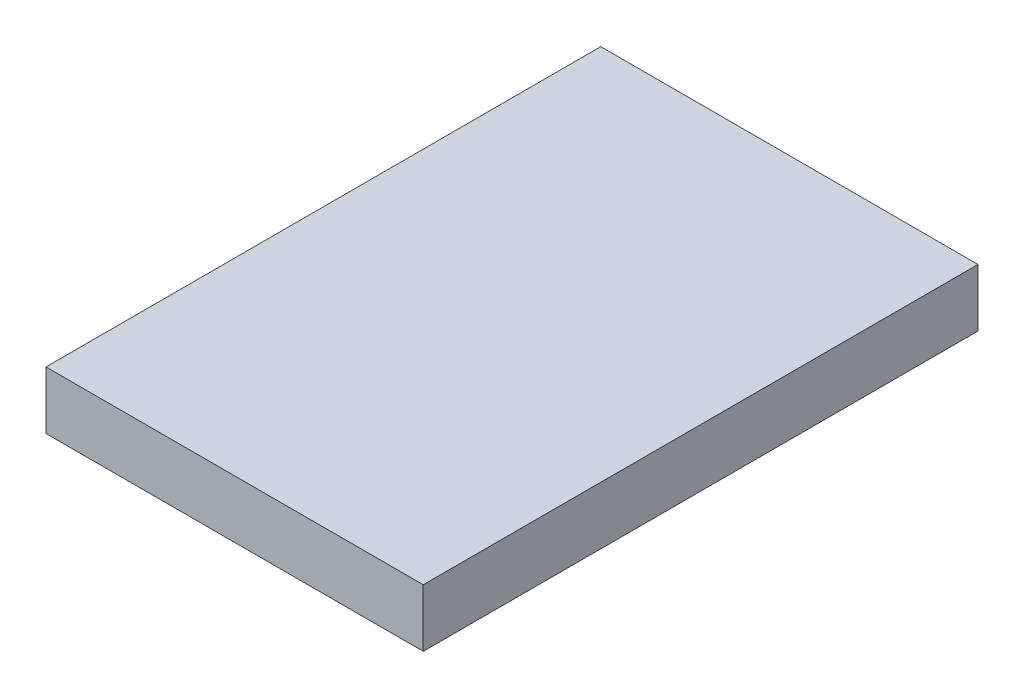
SolidWorks part; units mm, degrees
ref_plane "Front Plane" through (0, 0, 0) normal (0, 0, 1) x (1, 0, 0)
ref_plane "Top Plane" through (0, 0, 0) normal (0, 1, 0) x (1, 0, 0)
ref_plane "Right Plane" through (0, 0, 0) normal (1, 0, 0) x (0, 0, -1)
sketch "Sketch1" plane through (0, 0, 0) normal (0, 1, 0) x (1, 0, 0)
  line L1 (0, 0) -> (34, 0)
  line L2 (0, 0) -> (0, 50)
  line L3 (0, 50) -> (34, 50)
  line L4 (34, 0) -> (34, 50)
  dimension "D1" = 50
  dimension "D2" = 34
extrude "Boss-Extrude1" add sketch "Sketch1" along normal blind 5.2
